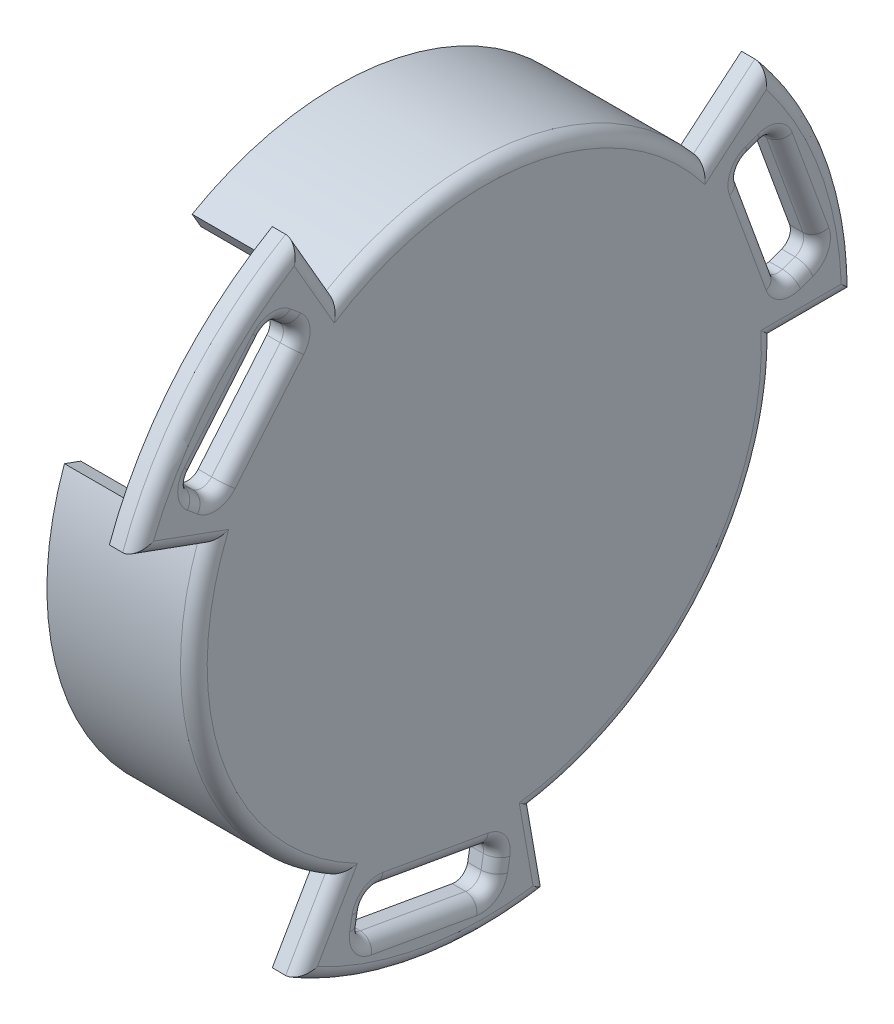
SolidWorks part; units mm, degrees
ref_plane "Front Plane" through (0, 0, 0) normal (0, 0, 1) x (1, 0, 0)
ref_plane "Top Plane" through (0, 0, 0) normal (0, 1, 0) x (1, 0, 0)
ref_plane "Right Plane" through (0, 0, 0) normal (1, 0, 0) x (0, 0, -1)
sketch "Sketch1" plane through (0, 0, 0) normal (1, 0, 0) x (0, 0, -1)
  circle A0 centre (0, 0) radius 21.75
  dimension "D1" = 43.5
extrude "Boss-Extrude1" add sketch "Sketch1" along normal blind 1 contours A0
sketch "Sketch2" plane through (0, 0, 0) normal (-1, 0, 0) x (0, 0, 1)
  circle A3 centre (0, 0) radius 18
  dimension "D1" = 36
extrude "Boss-Extrude2" add sketch "Sketch2" along normal blind 1.5 draft 40 contours A3
sketch "Sketch3" plane through (0, 0, 0) normal (-1, 0, 0) x (0, 0, 1)
  circle A2 centre (0, 0) radius 20.45
  circle A3 centre (0, 0) radius 20.45
  circle M3 centre (0, 0) radius 21.75
  dimension "D1" = 1.3
extrude "Boss-Extrude3" add sketch "Sketch3" along normal blind 10 contours A3 M3
sketch "Sketch6" plane through (0, 0, 0) normal (0, 1, 0) x (1, 0, 0)
  line L1 (-10, 20.45) -> (-10, -20.45) construction
  line L4 (-10, 21.75) -> (-10, 19.75)
  line L5 (-10, 21.75) -> (-10, -21.75) construction
  line L6 (-10, 19.75) -> (-1, 18.5)
  line L8 (-1, 18.5) -> (-1, 21.75)
  line L9 (-1, 21.75) -> (-10, 21.75)
  dimension "D1" = 2
  dimension "D2" = 9
sketch "Sketch7" plane through (0, 0, 0) normal (0, 1, 0) x (1, 0, 0)
  line L0 (-10, 0) -> (1, 0) construction
  line L1 (-10, 21.75) -> (-10, -21.75) construction
  line L2 (1, -21.75) -> (1, 21.75) construction
revolve "Cut-Revolve1" cut sketch "Sketch6" angle 40 about L0
pattern_circular "CirPattern1" count 3 over 360 about axis through (0, 0, 0) along (1, 0, 0) of "Cut-Revolve1"
sketch "Sketch8" plane through (0, 0, 0) normal (0, 1, 0) x (1, 0, 0)
  line L0 (-1, 21.75) -> (1, 21.75)
  line L5 (-1, 21.75) -> (-1, 27.75)
  line L6 (-1, 27.75) -> (1, 27.75)
  line L7 (1, 27.75) -> (1, 21.75)
  dimension "D1" = 6
revolve "Revolve1" add sketch "Sketch8" angle 40 about L0
sketch "Sketch9" plane through (-1, 0, 0) normal (-1, 0, 0) x (0, 0, 1)
  line L0 (0, 0) -> (-20.6732, 7.5244) construction
  line L6 (-20.6732, 7.5244) -> (-22.3833, 2.826)
  line L7 (-22.3833, 2.826) -> (-25.2024, 3.852)
  line L8 (-25.2024, 3.852) -> (-21.7822, 13.249)
  line L9 (-21.7822, 13.249) -> (-18.9631, 12.2229)
  line L10 (-18.9631, 12.2229) -> (-20.6732, 7.5244)
  line L11 (-27.75, 0) -> (-21.75, 0) construction
  line L12 (-18.9596, 15.909) -> (-20.3727, 12.7359) construction
  line L13 (-21.2577, 17.8374) -> (-16.6615, 13.9806) construction
  line L14 (-23.7929, 3.339) -> (-24.75, 0) construction
  line L15 (-20.3727, 12.7359) -> (-23.7929, 3.339) construction
  circle A0 centre (-22.0828, 8.0375) radius 1.46 construction
  dimension "D1" = 22
  dimension "D2" = 10
  dimension "D3" = 3
extrude "Cut-Extrude1" cut sketch "Sketch9" against normal blind 10
fillet "Fillet5" radius 1 4 edges at (0, 3.852, -25.2024) (0, 2.826, -22.3833) (0, 12.2229, -18.9631) (0, 13.249, -21.7822)
pattern_circular "CirPattern3" count 3 over 360 about axis through (0, 0, 0) along (1, 0, 0) of "Revolve1", "Cut-Extrude1", "Fillet5"
fillet "Fillet6" radius 1 36 edges at (1, 15.909, -18.9596) (1, 9.4911, -26.0765) (1, 0, -24.75) (1, -13.9806, -16.6615) (1, -24.374, -4.2978) (1, -27.3284, 4.8187) (1, -21.4341, 12.375) (1, -7.4389, 20.4383) (1, 8.465, 23.2574) (1, 17.8374, 21.2577) (1, 21.4341, 12.375) (1, 21.4196, -3.7768) (1, 3.2014, -22.5584) (1, 3.339, -23.7929) (1, 4.0271, -24.827) (1, 8.5505, -23.4923) (1, 12.8736, -21.6072) (1, 12.7359, -20.3727) (1, 12.0479, -19.3385) (1, 7.5244, -20.6732) (1, -21.1368, 8.5067) (1, -22.2747, 9.0048) (1, -23.5144, 8.9259) (1, -24.6202, 4.3412) (1, -25.1491, -0.3453) (1, -24.0112, -0.8433) (1, -22.7716, -0.7645) (1, -21.6658, 3.8203) (1, 17.9354, 14.0517) (1, 18.9357, 14.7881) (1, 19.4873, 15.9011) (1, 16.0697, 19.1511) (1, 12.2756, 21.9524) (1, 11.2753, 21.216) (1, 10.7237, 20.103) (1, 14.1413, 16.853)
